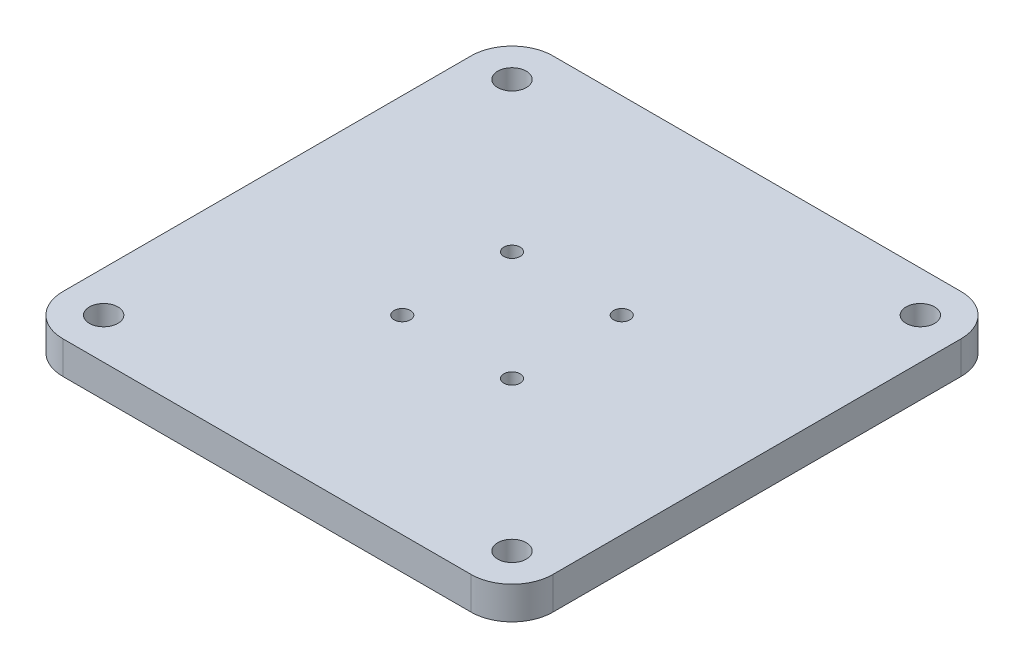
SolidWorks part; units mm, degrees
material "AISI 304"
ref_plane "前视基准面" through (0, 0, 0) normal (0, 0, 1) x (1, 0, 0)
ref_plane "上视基准面" through (0, 0, 0) normal (0, 1, 0) x (1, 0, 0)
ref_plane "右视基准面" through (0, 0, 0) normal (1, 0, 0) x (0, 0, -1)
sketch "草图1" plane through (0, 0, 0) normal (0, 1, 0) x (1, 0, 0)
  line L0 (0, 26.8858) -> (0, -28.1964) construction
  line L1 (-38.7424, 0) -> (33.1927, 0) construction
  line L2 (0, 0) -> (-13.435, 13.435) construction
  line L4 (-60, 60) -> (60, 60)
  line L5 (-60, 60) -> (-60, -60)
  line L6 (-60, -60) -> (60, -60)
  line L7 (60, 60) -> (60, -60)
  line L8 (-60, 60) -> (60, -60) construction
  line L9 (-60, -60) -> (60, 60) construction
  circle A0 centre (0, 0) radius 19 construction
  circle A1 centre (-13.435, 13.435) radius 2
  circle A2 centre (13.435, 13.435) radius 2
  circle A3 centre (13.435, -13.435) radius 2
  circle A4 centre (-13.435, -13.435) radius 2
  point P18 (0, 0)
  dimension "D1" = 38
  dimension "D3" = 4
  dimension "D2" = 45
  dimension "D5" = 120
  dimension "D6" = 120
  dimension "D4" = 4
extrude "凸台-拉伸1" add sketch "草图1" along normal blind 8
sketch "草图2" plane through (0, 8, 0) normal (0, 1, 0) x (1, 0, 0)
  line L0 (0, 85.6705) -> (0, -67.0248) construction
  line L1 (-100.2556, 0) -> (103.6275, 0) construction
  circle A0 centre (-50, 50) radius 3.5
  circle A1 centre (50, 50) radius 3.5
  circle A2 centre (50, -50) radius 3.5
  circle A3 centre (-50, -50) radius 3.5
  dimension "D1" = 7
  dimension "D2" = 50
  dimension "D3" = 50
extrude "切除-拉伸1" cut sketch "草图2" against normal blind 10
sketch "草图3" plane through (0, 0, 0) normal (0, -1, 0) x (1, 0, 0)
  circle A0 centre (-13.435, 13.435) radius 3.5
  circle A2 centre (13.435, 13.435) radius 3.5
  circle A3 centre (-13.435, -13.435) radius 3.5
  circle A4 centre (13.435, -13.435) radius 3.5
  dimension "D1" = 7
  dimension "D2" = 7
  dimension "D3" = 7
  dimension "D4" = 7
extrude "切除-拉伸2" cut sketch "草图3" against normal blind 4
fillet "圆角1" radius 10 4 edges at (60, 4, 60) (-60, 4, 60) (-60, 4, -60) (60, 4, -60)
